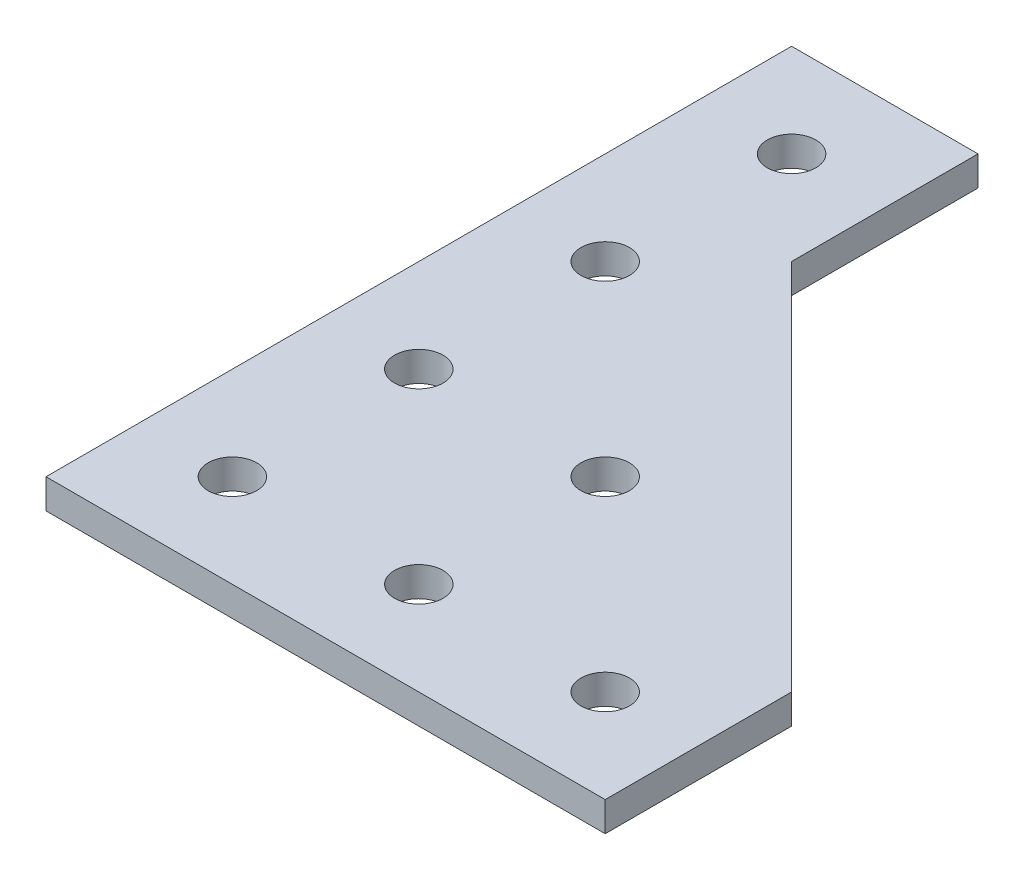
SolidWorks part; units mm, degrees
material "6061-T6 (SS)"
ref_plane "Front Plane" through (0, 0, 0) normal (0, 0, 1) x (1, 0, 0)
ref_plane "Top Plane" through (0, 0, 0) normal (0, 1, 0) x (1, 0, 0)
ref_plane "Right Plane" through (0, 0, 0) normal (1, 0, 0) x (0, 0, -1)
sketch "Sketch1" plane through (0, 0, 0) normal (0, 1, 0) x (1, 0, 0)
  line L0 (60, 20) -> (20, 60)
  line L1 (0, 0) -> (60, 0)
  line L2 (0, 0) -> (0, 80)
  line L3 (0, 80) -> (20, 80)
  line L4 (20, 80) -> (20, 60)
  line L5 (60, 20) -> (60, 0)
  line L6 (10, 10) -> (10, 70) construction
  line L7 (10, 10) -> (50, 10) construction
  circle A0 centre (30, 10) radius 2.6
  circle A1 centre (50, 10) radius 2.6
  circle A2 centre (30, 30) radius 2.6
  circle A3 centre (50, 30) radius 2.6 [skipped]
  circle A4 centre (10, 10) radius 2.6
  circle A5 centre (30, 50) radius 2.6 [skipped]
  circle A6 centre (50, 50) radius 2.6 [skipped]
  circle A7 centre (30, 70) radius 2.6 [skipped]
  circle A8 centre (50, 70) radius 2.6 [skipped]
  circle A9 centre (10, 30) radius 2.6
  circle A10 centre (10, 50) radius 2.6
  circle A11 centre (10, 70) radius 2.6
  dimension "D6" = 5.2
  dimension "D7" = 10
  dimension "D8" = 10
  dimension "D11" = 20
  dimension "D12" = 20
  dimension "D1" = 80
  dimension "D2" = 60
  dimension "D3" = 20
  dimension "D4" = 20
  dimension "D5" = 20
  dimension "D9" = 3
  dimension "D10" = 4
extrude "Boss-Extrude1" add sketch "Sketch1" along normal blind 3.175
